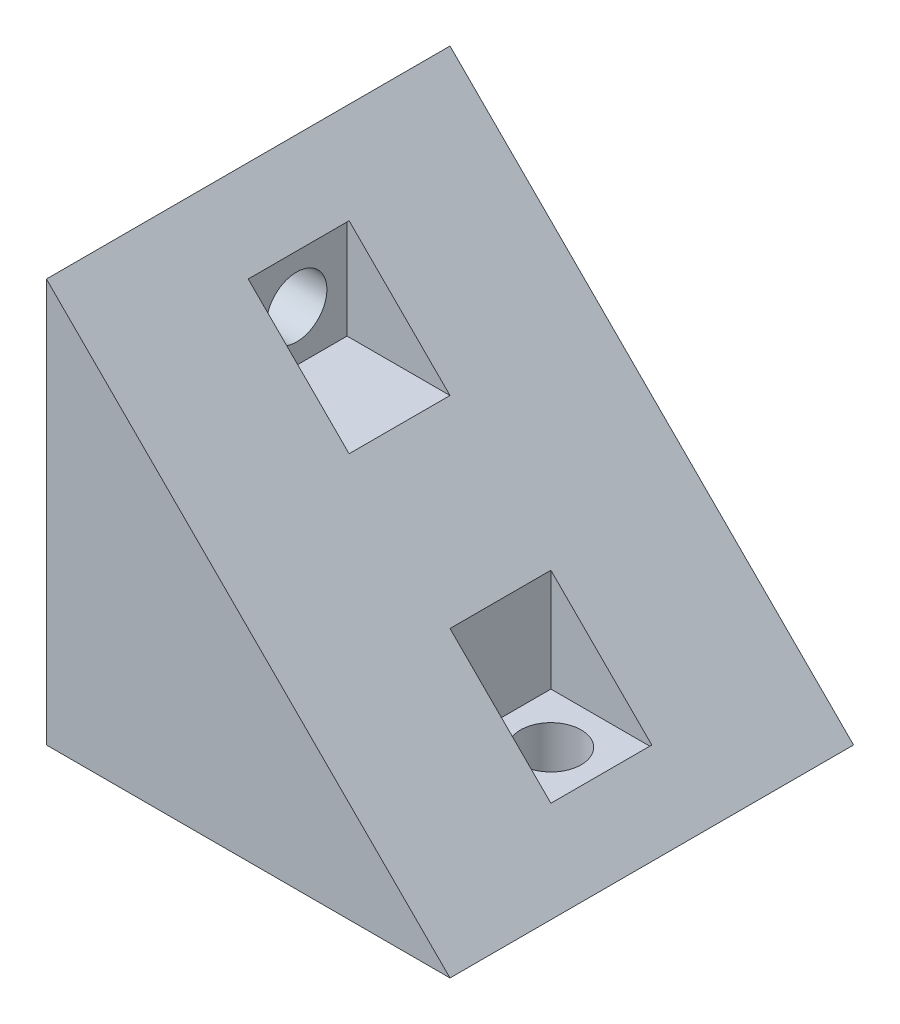
SolidWorks part; units mm, degrees
ref_plane "Plan de face" through (0, 0, 0) normal (0, 0, 1) x (1, 0, 0)
ref_plane "Plan de dessus" through (0, 0, 0) normal (0, 1, 0) x (1, 0, 0)
ref_plane "Plan de droite" through (0, 0, 0) normal (1, 0, 0) x (0, 0, -1)
sketch "Esquisse2" plane through (0, 0, 0) normal (0, 0, 1) x (1, 0, 0)
  line L0 (0, 0) -> (0, 40)
  line L1 (0, 40) -> (40, 0)
  line L2 (40, 0) -> (0, 0)
  dimension "D1" = 40
  dimension "D2" = 40
extrude "Boss.-Extru.1" add sketch "Esquisse2" along normal blind 40
sketch "Esquisse3" plane through (0, 0, 0) normal (0, -1, 0) x (1, 0, 0)
  line L0 (0, 40) -> (40, 40) construction
  line L3 (40, 40) -> (40, 0) construction
  circle A0 centre (30, 20) radius 3
  point P6 (40, 17.1366)
  point P7 (40, 17.2556)
  dimension "D3" = 6
  dimension "D1" = 20
  dimension "D2" = 10
extrude "Enlèv. mat.-Extru.1" cut sketch "Esquisse3" against normal up to next
sketch "Esquisse4" plane through (0, 0, 0) normal (-1, 0, 0) x (0, 0, 1)
  line L0 (0, 40) -> (0, 0) construction
  line L1 (40, 40) -> (0, 40) construction
  circle A0 centre (20, 30) radius 3
  dimension "D3" = 6
  dimension "D1" = 20
  dimension "D2" = 10
extrude "Enlèv. mat.-Extru.2" cut sketch "Esquisse4" against normal up to next
ref_plane "Plan4" through (4.8, 0, 0) normal (-1, 0, 0) x (0, 0, 1)
ref_plane "Plan5" through (0, 4.8, 0) normal (0, -1, 0) x (0, 0, 1)
sketch "Esquisse9" plane through (4.8, 0, 0) normal (-1, 0, 0) x (0, 0, 1)
  line L1 (15, 25) -> (25, 25)
  line L2 (15, 25) -> (15, 35)
  line L3 (15, 35) -> (25, 35)
  line L4 (25, 25) -> (25, 35)
  line L5 (15, 25) -> (25, 35) construction
  line L6 (15, 35) -> (25, 25) construction
  point P0 (20, 30)
  dimension "D1" = 10
  dimension "D2" = 10
extrude "Enlèv. mat.-Extru.4" cut sketch "Esquisse9" against normal up to next
sketch "Esquisse10" plane through (0, 4.8, 0) normal (0, -1, 0) x (0, 0, 1)
  line L1 (15, -35) -> (25, -35)
  line L2 (15, -35) -> (15, -25)
  line L3 (15, -25) -> (25, -25)
  line L4 (25, -35) -> (25, -25)
  line L5 (15, -35) -> (25, -25) construction
  line L6 (15, -25) -> (25, -35) construction
  point P0 (20, -30)
  dimension "D1" = 10
  dimension "D2" = 10
extrude "Enlèv. mat.-Extru.5" cut sketch "Esquisse10" against normal up to next
